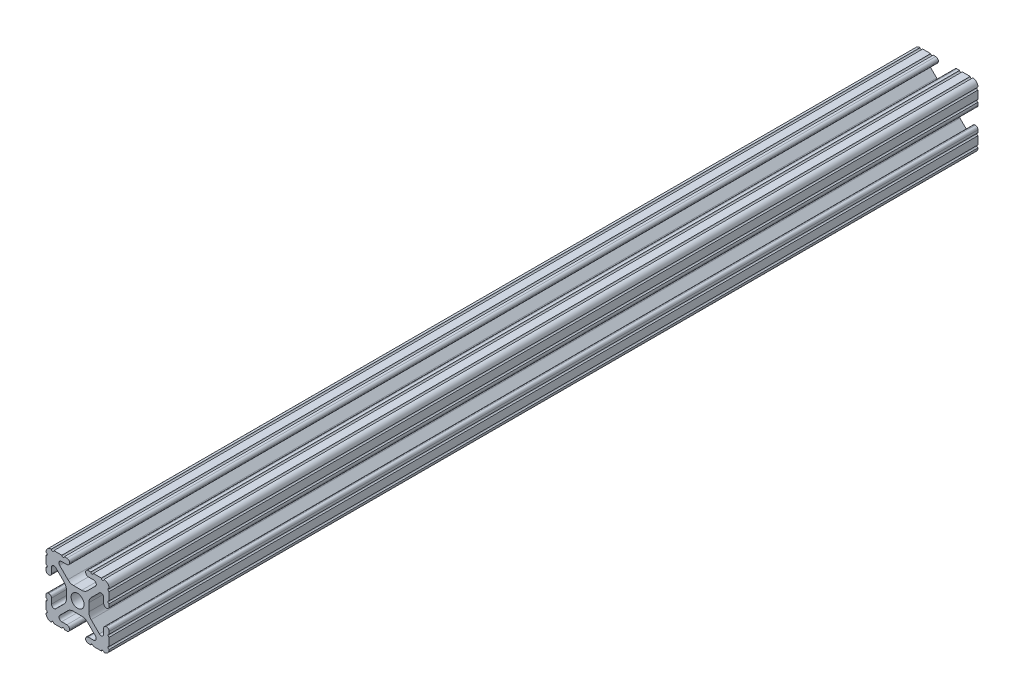
SolidWorks part; units mm, degrees
ref_plane "Front" through (0, 0, 0) normal (0, 0, 1) x (1, 0, 0)
ref_plane "Top" through (0, 0, 0) normal (0, 1, 0) x (1, 0, 0)
ref_plane "Right" through (0, 0, 0) normal (1, 0, 0) x (0, 0, -1)
sketch "Sketch1" plane through (0, 0, 0) normal (0, 0, 1) x (1, 0, 0)
  line L0 (-7.5107, 9.4563) -> (7.5107, 9.4563) construction
  line L1 (-7.4968, -9.4098) -> (7.4968, -9.4098) construction
  line L88 (-7.1797, -8.6452) -> (-3.9523, -5.4237)
  line L89 (-1.7093, -4.4958) -> (1.7093, -4.4958)
  line L90 (3.9523, -5.4237) -> (7.1797, -8.6452)
  line L91 (6.4164, -10.4902) -> (4.2875, -10.4902)
  line L92 (3.2385, -11.5392) -> (3.2385, -11.651)
  line L93 (4.2875, -12.7) -> (5.3171, -12.7)
  line L94 (6.3331, -12.7) -> (9.5504, -12.7)
  line L95 (12.7, -9.5504) -> (12.7, -6.3331)
  line L96 (12.7, -5.3171) -> (12.7, -4.2875)
  line L97 (11.651, -3.2385) -> (11.5392, -3.2385)
  line L98 (10.4902, -4.2875) -> (10.4902, -6.4021)
  line L99 (8.7371, -7.1294) -> (5.441, -3.8408)
  line L100 (4.5085, -1.5932) -> (4.5085, 1.5932)
  line L101 (5.441, 3.8408) -> (8.7371, 7.1294)
  line L102 (10.4902, 6.4021) -> (10.4902, 4.2875)
  line L103 (11.5392, 3.2385) -> (11.651, 3.2385)
  line L104 (12.7, 4.2875) -> (12.7, 5.3171)
  line L105 (12.7, 6.3331) -> (12.7, 9.5504)
  line L106 (9.5504, 12.7) -> (6.3331, 12.7)
  line L107 (5.3171, 12.7) -> (4.2875, 12.7)
  line L108 (3.2385, 11.651) -> (3.2385, 11.5392)
  line L109 (4.2875, 10.4902) -> (6.4768, 10.4902)
  line L110 (7.207, 8.7244) -> (3.8983, 5.4232)
  line L111 (1.6558, 4.4958) -> (-1.6558, 4.4958)
  line L112 (-3.8983, 5.4232) -> (-7.207, 8.7244)
  line L113 (-6.4768, 10.4902) -> (-4.2875, 10.4902)
  line L114 (-3.2385, 11.5392) -> (-3.2385, 11.651)
  line L115 (-4.2875, 12.7) -> (-5.3171, 12.7)
  line L116 (-6.3331, 12.7) -> (-9.5504, 12.7)
  line L117 (-12.7, 9.5504) -> (-12.7, 6.3331)
  line L118 (-12.7, 5.3171) -> (-12.7, 4.2875)
  line L119 (-11.651, 3.2385) -> (-11.5392, 3.2385)
  line L120 (-10.4902, 4.2875) -> (-10.4902, 6.4021)
  line L121 (-8.7371, 7.1294) -> (-5.441, 3.8408)
  line L122 (-4.5085, 1.5932) -> (-4.5085, -1.5932)
  line L123 (-5.441, -3.8408) -> (-8.7371, -7.1294)
  line L124 (-10.4902, -6.4021) -> (-10.4902, -4.2875)
  line L125 (-11.5392, -3.2385) -> (-11.651, -3.2385)
  line L126 (-12.7, -4.2875) -> (-12.7, -5.3171)
  line L127 (-12.7, -6.3331) -> (-12.7, -9.5504)
  line L128 (-9.5504, -12.7) -> (-6.3331, -12.7)
  line L129 (-5.3171, -12.7) -> (-4.2875, -12.7)
  line L130 (-3.2385, -11.651) -> (-3.2385, -11.5392)
  line L131 (-4.2875, -10.4902) -> (-6.4164, -10.4902)
  circle A1 centre (0, 0) radius 2.6035
  arc A104 (-7.1797, -8.6452) -> (-6.4164, -10.4902) centre (-6.4164, -9.4098) ccw
  arc A105 (-1.7093, -4.4958) -> (-3.9523, -5.4237) centre (-1.7093, -7.6708) ccw
  arc A106 (3.9523, -5.4237) -> (1.7093, -4.4958) centre (1.7093, -7.6708) ccw
  arc A107 (6.4164, -10.4902) -> (7.1797, -8.6452) centre (6.4164, -9.4098) ccw
  arc A108 (4.2875, -10.4902) -> (3.2385, -11.5392) centre (4.2875, -11.5392) ccw
  arc A109 (3.2385, -11.651) -> (4.2875, -12.7) centre (4.2875, -11.651) ccw
  arc A110 (6.3331, -12.7) -> (5.3171, -12.7) centre (5.8251, -12.7) ccw
  arc A111 (10.5664, -12.6998) -> (9.5504, -12.7) centre (10.0584, -12.7) ccw
  arc A112 (10.5664, -12.6998) -> (12.6998, -10.5664) centre (10.5918, -10.5918) ccw
  arc A113 (12.7, -9.5504) -> (12.6998, -10.5664) centre (12.7, -10.0584) ccw
  arc A114 (12.7, -5.3171) -> (12.7, -6.3331) centre (12.7, -5.8251) ccw
  arc A115 (12.7, -4.2875) -> (11.651, -3.2385) centre (11.651, -4.2875) ccw
  arc A116 (11.5392, -3.2385) -> (10.4902, -4.2875) centre (11.5392, -4.2875) ccw
  arc A117 (8.7371, -7.1294) -> (10.4902, -6.4021) centre (9.4628, -6.4021) ccw
  arc A118 (4.5085, -1.5932) -> (5.441, -3.8408) centre (7.6835, -1.5932) ccw
  arc A119 (5.441, 3.8408) -> (4.5085, 1.5932) centre (7.6835, 1.5932) ccw
  arc A120 (10.4902, 6.4021) -> (8.7371, 7.1294) centre (9.4628, 6.4021) ccw
  arc A121 (10.4902, 4.2875) -> (11.5392, 3.2385) centre (11.5392, 4.2875) ccw
  arc A122 (11.651, 3.2385) -> (12.7, 4.2875) centre (11.651, 4.2875) ccw
  arc A123 (12.7, 6.3331) -> (12.7, 5.3171) centre (12.7, 5.8251) ccw
  arc A124 (12.6998, 10.5664) -> (12.7, 9.5504) centre (12.7, 10.0584) ccw
  arc A125 (12.6998, 10.5664) -> (10.5664, 12.6998) centre (10.5918, 10.5918) ccw
  arc A126 (9.5504, 12.7) -> (10.5664, 12.6998) centre (10.0584, 12.7) ccw
  arc A127 (5.3171, 12.7) -> (6.3331, 12.7) centre (5.8251, 12.7) ccw
  arc A128 (4.2875, 12.7) -> (3.2385, 11.651) centre (4.2875, 11.651) ccw
  arc A129 (3.2385, 11.5392) -> (4.2875, 10.4902) centre (4.2875, 11.5392) ccw
  arc A130 (7.207, 8.7244) -> (6.4768, 10.4902) centre (6.4768, 9.4563) ccw
  arc A131 (1.6558, 4.4958) -> (3.8983, 5.4232) centre (1.6558, 7.6708) ccw
  arc A132 (-3.8983, 5.4232) -> (-1.6558, 4.4958) centre (-1.6558, 7.6708) ccw
  arc A133 (-6.4768, 10.4902) -> (-7.207, 8.7244) centre (-6.4768, 9.4563) ccw
  arc A134 (-4.2875, 10.4902) -> (-3.2385, 11.5392) centre (-4.2875, 11.5392) ccw
  arc A135 (-3.2385, 11.651) -> (-4.2875, 12.7) centre (-4.2875, 11.651) ccw
  arc A136 (-6.3331, 12.7) -> (-5.3171, 12.7) centre (-5.8251, 12.7) ccw
  arc A137 (-10.5664, 12.6998) -> (-9.5504, 12.7) centre (-10.0584, 12.7) ccw
  arc A138 (-10.5664, 12.6998) -> (-12.6998, 10.5664) centre (-10.5918, 10.5918) ccw
  arc A139 (-12.7, 9.5504) -> (-12.6998, 10.5664) centre (-12.7, 10.0584) ccw
  arc A140 (-12.7, 5.3171) -> (-12.7, 6.3331) centre (-12.7, 5.8251) ccw
  arc A141 (-12.7, 4.2875) -> (-11.651, 3.2385) centre (-11.651, 4.2875) ccw
  arc A142 (-11.5392, 3.2385) -> (-10.4902, 4.2875) centre (-11.5392, 4.2875) ccw
  arc A143 (-8.7371, 7.1294) -> (-10.4902, 6.4021) centre (-9.4628, 6.4021) ccw
  arc A144 (-4.5085, 1.5932) -> (-5.441, 3.8408) centre (-7.6835, 1.5932) ccw
  arc A145 (-5.441, -3.8408) -> (-4.5085, -1.5932) centre (-7.6835, -1.5932) ccw
  arc A146 (-10.4902, -6.4021) -> (-8.7371, -7.1294) centre (-9.4628, -6.4021) ccw
  arc A147 (-10.4902, -4.2875) -> (-11.5392, -3.2385) centre (-11.5392, -4.2875) ccw
  arc A148 (-11.651, -3.2385) -> (-12.7, -4.2875) centre (-11.651, -4.2875) ccw
  arc A149 (-12.7, -6.3331) -> (-12.7, -5.3171) centre (-12.7, -5.8251) ccw
  arc A150 (-12.6998, -10.5664) -> (-12.7, -9.5504) centre (-12.7, -10.0584) ccw
  arc A151 (-12.6998, -10.5664) -> (-10.5664, -12.6998) centre (-10.5918, -10.5918) ccw
  arc A152 (-9.5504, -12.7) -> (-10.5664, -12.6998) centre (-10.0584, -12.7) ccw
  arc A153 (-5.3171, -12.7) -> (-6.3331, -12.7) centre (-5.8251, -12.7) ccw
  arc A154 (-4.2875, -12.7) -> (-3.2385, -11.651) centre (-4.2875, -11.651) ccw
  arc A155 (-3.2385, -11.5392) -> (-4.2875, -10.4902) centre (-4.2875, -11.5392) ccw
extrude "Boss-Extrude1" add sketch "Sketch1" along normal mid plane 349.25
